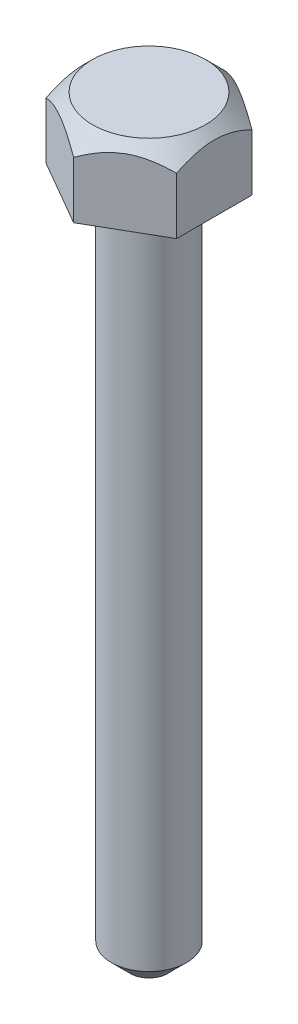
SolidWorks part; units mm, degrees
ref_plane "Front Plane" through (0, 0, 0) normal (0, 0, 1) x (1, 0, 0)
ref_plane "Top Plane" through (0, 0, 0) normal (0, 1, 0) x (1, 0, 0)
ref_plane "Right Plane" through (0, 0, 0) normal (1, 0, 0) x (0, 0, -1)
sketch "Sketch1" plane through (0, 0, 0) normal (0, 0, 1) x (1, 0, 0)
  line L0 (0, 0) -> (0, 31.75) construction
  line L1 (0, 31.75) -> (-2.3813, 31.75)
  line L2 (-3.175, 30.9563) -> (-3.175, 28.575)
  line L3 (-3.175, 28.575) -> (-1.5875, 28.575)
  line L4 (-1.5875, 28.575) -> (-1.5875, 0.7937)
  line L5 (-0.7937, 0) -> (0, 0)
  line L6 (-2.3813, 31.75) -> (-3.175, 30.9563)
  line L7 (-1.5875, 0.7937) -> (-0.7937, 0)
  line L8 (0, 0) -> (0, 31.75)
  point P4 (-3.175, 31.75)
  point P7 (-1.5875, 0)
  dimension "D1" = 1.5875
  dimension "D2" = 1.5875
  dimension "D3" = 3.175
  dimension "D4" = 28.575
revolve "Revolve1" add sketch "Sketch1" angle 360 about L0
sketch "Sketch2" plane through (0, 31.75, 0) normal (0, 1, 0) x (1, 0, 0)
  line L1 (0, 3.175) -> (-2.7496, 1.5875)
  line L2 (-2.7496, 1.5875) -> (-2.7496, -1.5875)
  line L3 (-2.7496, -1.5875) -> (0, -3.175)
  line L4 (0, -3.175) -> (2.7496, -1.5875)
  line L5 (2.7496, -1.5875) -> (2.7496, 1.5875)
  line L6 (2.7496, 1.5875) -> (0, 3.175)
  circle A0 centre (0, 0) radius 2.7496 construction
  circle A1 centre (0, 0) radius 3.175 construction
  circle A2 centre (0, 0) radius 3.175
extrude "Cut-Extrude1" cut sketch "Sketch2" against normal up to next contours L1 A2 | L6 A2 | L5 A2 | L4 A2 | L3 A2 | L2 A2
equation "\".af\"=0.260261"
